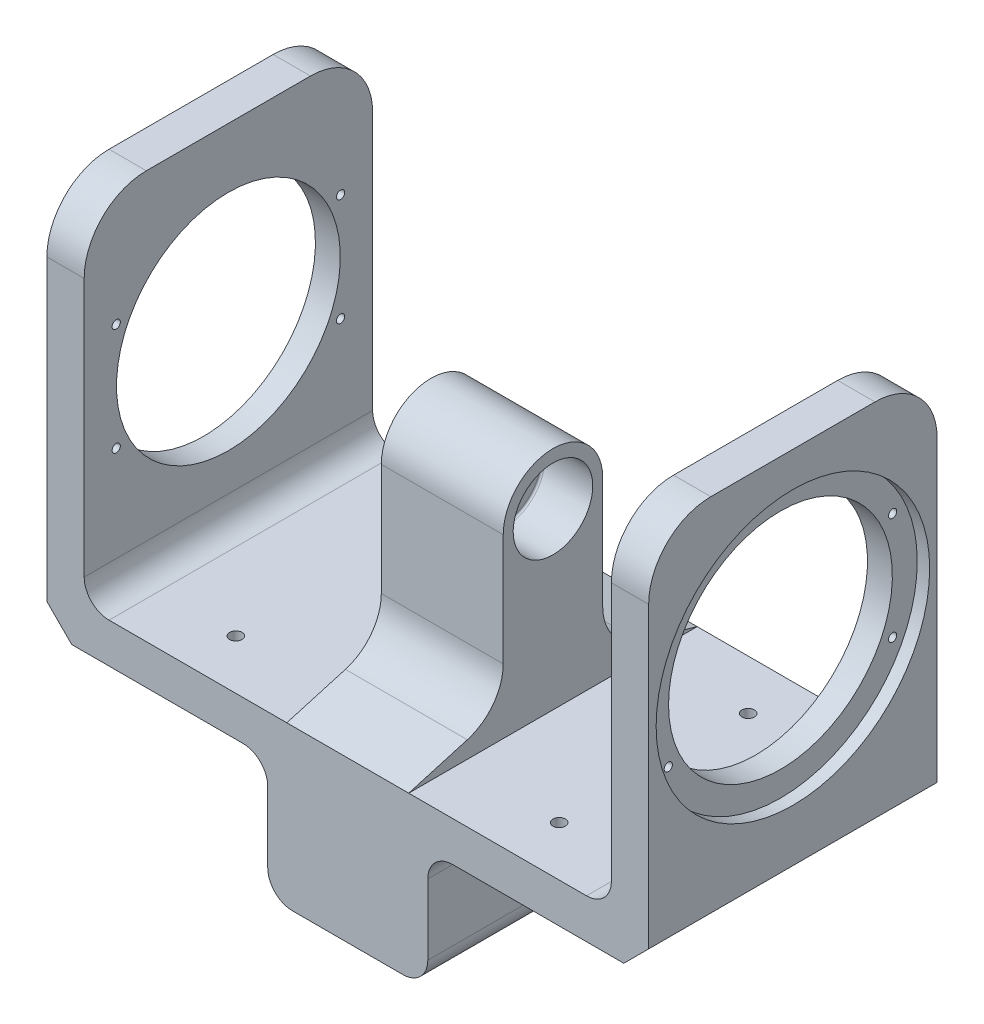
SolidWorks part; units mm, degrees
material "1060 Alloy"
ref_plane "Front Plane" through (0, 0, 0) normal (0, 0, 1) x (1, 0, 0)
ref_plane "Top Plane" through (0, 0, 0) normal (0, 1, 0) x (1, 0, 0)
ref_plane "Right Plane" through (0, 0, 0) normal (1, 0, 0) x (0, 0, -1)
sketch "Sketch1" plane through (0, 0, 0) normal (0, 0, 1) x (1, 0, 0)
  line L0 (0, 0) -> (-106, 0)
  line L1 (55, 0) -> (-55, 0) construction
  line L3 (-121, 0) -> (-121, 155)
  line L4 (-121, 155) -> (-106, 155)
  line L5 (-106, 155) -> (-106, 16)
  line L7 (-106, 16) -> (-24.51, 16)
  line L9 (-24.51, 16) -> (-24.51, 107)
  line L10 (-24.51, 107) -> (0, 107)
  line L11 (0, -55) -> (0, 55) construction
  line L12 (0, 107) -> (0, 0)
  line L13 (-121, 0) -> (-106, 0)
  dimension "D1" = 24.51
  dimension "D2" = 91
  dimension "D4" = 121
  dimension "D5" = 15
  dimension "D6" = 16
  dimension "D8" = 48
extrude "Boss-Extrude1" add sketch "Sketch1" against normal blind 116
sketch "Sketch5" plane through (-24.51, 0, 0) normal (-1, 0, 0) x (0, 0, 1)
  line L0 (-116, 107) -> (0, 107) construction
  line L1 (0, 107) -> (0, 16) construction
  circle A0 centre (-58, 86) radius 16
  dimension "D3" = 32
  dimension "D1" = 21
  dimension "D2" = 58
extrude "Cut-Extrude1" cut sketch "Sketch5" against normal blind 20
sketch "Sketch6" plane through (-4.51, 0, 0) normal (-1, 0, 0) x (0, 0, 1)
  circle A0 centre (-58, 86) radius 10
  dimension "D1" = 20
extrude "Cut-Extrude2" cut sketch "Sketch6" against normal up to next
sketch "Sketch8" plane through (-106, 0, 0) normal (1, 0, 0) x (0, 0, -1)
  circle A0 centre (58, 86) radius 45
  circle A1 centre (58, 86) radius 10 construction
  dimension "D1" = 90
extrude "Cut-Extrude4" cut sketch "Sketch8" against normal up to next
sketch "Sketch10" plane through (0, 0, 0) normal (1, 0, 0) x (0, 0, -1)
  line L1 (0, 66.55) -> (0, -66.55) construction
  line L2 (116, 0) -> (116, 107) construction
  line L5 (0, 16) -> (0, 107)
  line L6 (116, 107) -> (0, 107) construction
  line L7 (0, 107) -> (116, 107)
  line L8 (116, 107) -> (116, 16)
  line L9 (38, 87) -> (38, 42.0316)
  line L11 (25, 16) -> (57, 16)
  line L13 (116, 0) -> (0, 0) construction
  line L14 (25, 16) -> (0, 16)
  line L15 (0, 107) -> (116, 107)
  line L16 (116, 16) -> (57, 16)
  line L17 (23.5612, 22.8203) -> (0, 16)
  line L18 (78, 87) -> (78, 42.0316)
  line L19 (92.4388, 22.8203) -> (116, 16)
  arc A0 (38, 87) -> (78, 87) centre (58, 87) cw
  arc A1 (78, 42.0316) -> (92.4388, 22.8203) centre (98, 42.0316) ccw
  arc A2 (38, 42.0316) -> (23.5612, 22.8203) centre (18, 42.0316) cw
  point P18 (58, 107)
  point P23 (78, 27)
  point P27 (38, 27)
  dimension "D2" = 20
  dimension "D3" = 60
  dimension "D4" = 20
  dimension "D1" = 16
extrude "Cut-Extrude5" cut sketch "Sketch10" against normal up to surface (106 mm away)
fillet "Fillet3" radius 25 2 edges at (-113.5, 155, -116) (-113.5, 155, 0)
hole_wizard "M6x1.0 Tapped Hole1" positions "Sketch16" profile "Sketch17" tap size "M6x1.0" standard "ANSI Metric" end condition up to next
sketch "Sketch16" plane through (0, 0, 0) normal (0, -1, 0) x (-1, 0, 0)
  line L0 (0, 116) -> (0, 0) construction
  line L1 (121, 116) -> (0, 116) construction
  line L2 (121, 0) -> (0, 0) construction
  point P0 (65, 20)
  point P2 (65, 96)
  dimension "D1" = 65
  dimension "D2" = 20
  dimension "D3" = 20
sketch "Sketch17" plane through (-65, 0, -20) normal (1, 0, 0) x (0, 0, -1)
  line L0 (0, 0) -> (0, 16)
  line L1 (0, 16) -> (2.5, 16)
  line L2 (2.5, 16) -> (2.5, 0)
  line L5 (2.5, 0) -> (0, 0)
  line L11 (0, -6.35) -> (0, 107.95) construction
  dimension "Thread Major Dia." = 5
  dimension "Thru Tap Drill Depth" = 16
sketch "Sketch21" plane through (-121, 0, 0) normal (-1, 0, 0) x (0, 0, 1)
  circle A0 centre (-58, 86) radius 55
  circle A1 centre (-58, 86) radius 45 construction
  dimension "D1" = 10
extrude "Cut-Extrude7" cut sketch "Sketch21" against normal blind 5
hole_wizard "M4x0.7 Tapped Hole1" positions "Sketch22" profile "Sketch23" tap size "M4x0.7" standard "ANSI Metric"
sketch "Sketch22" plane through (-116, 0, 0) normal (-1, 0, 0) x (0, 0, 1)
  circle A0 centre (-58, 86) radius 50
  point P0 (-103.1086, 107.5689)
  point P2 (-12.8914, 107.5689)
  point P4 (-12.8914, 64.4311)
  point P6 (-103.1086, 64.4311)
  dimension "D1" = 100
sketch "Sketch23" plane through (-116, 107.5689, -103.1086) normal (0, 1, 0) x (0, 0, 1)
  line L0 (0, 0) -> (0, 10.9904)
  line L1 (0, 10.9904) -> (1.65, 9.999)
  line L2 (1.65, 9.999) -> (1.65, 0)
  line L5 (1.65, 0) -> (0, 0)
  line L10 (0, 10.9904) -> (-1.65, 9.999) construction
  line L11 (0, -6.35) -> (0, 107.95) construction
  dimension "Tap Drill Dia." = 3.3
  dimension "Tap Drill Depth" = 9.999
  dimension "Drill Angle" = 118
mirror "Mirror1" about plane through (0, 107, -116) normal (1, 0, 0) of bodies 128
fillet "Fillet4" radius 0.8 2 edges at (4.51, 70, -58) (-4.51, 70, -58)
chamfer "Chamfer1" distance 10 angle 45 2 edges at (-121, 0, -58) (121, 0, -58)
sketch "Sketch25" plane through (0, 0, 0) normal (0, 0, 1) x (1, 0, 0)
  line L0 (-111, 0) -> (111, 0) construction
  line L1 (32.178, 0) -> (-32.178, 0)
  line L2 (32.178, 0) -> (32.178, -48.356)
  line L3 (32.178, -48.356) -> (-32.178, -48.356)
  line L4 (-32.178, 0) -> (-32.178, -48.356)
  line L5 (-24.51, 16) -> (24.51, 16) construction
  point P6 (0, 0)
  dimension "D1" = 64.356
  dimension "D2" = 64.356
extrude "Boss-Extrude2" add sketch "Sketch25" against normal up to surface (116 mm away) up to face at (0, 50.3333, -116)
sketch "Sketch27" plane through (0, 0, -116) normal (0, 0, -1) x (-1, 0, 0)
  line L0 (32.178, -48.356) -> (-32.178, -48.356) construction
  line L1 (-21.0503, -43.356) -> (21.0502, -43.356)
  line L2 (-27.178, -37.2283) -> (-27.178, 4.8722)
  line L3 (-21.0503, 11) -> (21.0502, 11)
  line L4 (27.178, -37.2283) -> (27.178, 4.8722)
  line L5 (-27.178, -43.356) -> (27.178, 11) construction
  line L6 (-27.178, 11) -> (27.178, -43.356) construction
  arc A0 (-21.0503, -43.356) -> (-27.178, -37.2283) centre (-21.0503, -37.2283) cw
  arc A1 (21.0502, -43.356) -> (27.178, -37.2283) centre (21.0502, -37.2283) ccw
  arc A2 (21.0502, 11) -> (27.178, 4.8722) centre (21.0502, 4.8722) cw
  arc A3 (-27.178, 4.8722) -> (-21.0503, 11) centre (-21.0503, 4.8722) cw
  point P0 (0, -16.178)
  point P7 (0, 0)
  dimension "D4" = 6.1277
  dimension "D1" = 32.178
  dimension "D2" = 54.356
  dimension "D3" = 54.356
extrude "Cut-Extrude8" cut sketch "Sketch27" against normal offset from surface (106 mm away) 10 up to face at (0, 31.7055, 0)
fillet "Fillet6" radius 10 2 edges at (32.178, 0, -58) (-32.178, 0, -58)
fillet "Fillet7" radius 10 2 edges at (32.178, -48.356, -58) (-32.178, -48.356, -58)
fillet "Fillet8" radius 10 2 edges at (106, 16, -58) (-106, 16, -58)
